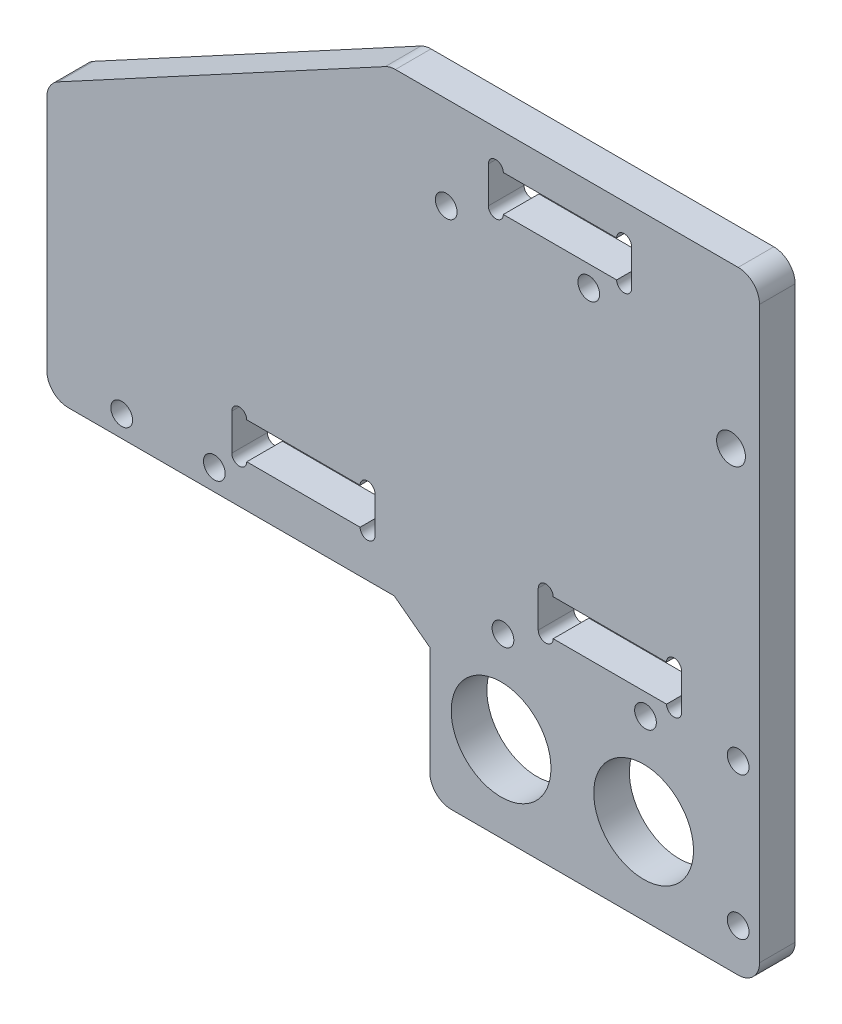
SolidWorks part; units mm, degrees
material "Thornel Mat VMA"
ref_plane "前视基准面" through (0, 0, 0) normal (0, 0, 1) x (1, 0, 0)
ref_plane "上视基准面" through (0, 0, 0) normal (0, 1, 0) x (1, 0, 0)
ref_plane "右视基准面" through (0, 0, 0) normal (1, 0, 0) x (0, 0, -1)
other "Configuration Table"
sketch "草图1" plane through (0, 0, 0) normal (0, 0, 1) x (1, 0, 0)
  line L0 (0, 0) -> (-46.2626, 16.8382)
  line L1 (-46.2626, 16.8382) -> (-46.2626, 27.95)
  line L2 (-46.2626, 27.95) -> (-86.2626, 27.95)
  line L3 (-86.2626, 27.95) -> (-100, 32.95)
  line L4 (-100, 32.95) -> (-100, 87)
  line L5 (-100, 87) -> (0, 87)
  line L6 (0, 87) -> (0, 0)
  line L11 (-127.5, 27.95) -> (-80, 27.95) construction
  dimension "D1" = 87
  dimension "D2" = 100
  dimension "D3" = 70
  dimension "D4" = 40
  dimension "D5" = 5
extrude "凸台-拉伸1" add sketch "草图1" along normal blind 5
sketch "草图4" plane through (0, 0, 0) normal (0, 0, -1) x (-1, 0, 0)
  line L1 (17.95, 81.05) -> (38.05, 81.05)
  line L2 (17.95, 81.05) -> (17.95, 75.95)
  line L3 (17.95, 75.95) -> (38.05, 75.95)
  line L4 (38.05, 81.05) -> (38.05, 75.95)
  line L5 (17.95, 81.05) -> (38.05, 75.95) construction
  line L6 (17.95, 75.95) -> (38.05, 81.05) construction
  line L7 (0, 0) -> (0, 87) construction
  line L8 (0, 87) -> (100, 87) construction
  point P0 (28, 78.5)
  dimension "D1" = 8.5
  dimension "D2" = 5.1
  dimension "D3" = 20.1
  dimension "D4" = 28
extrude "切除-拉伸3" cut sketch "草图4" against normal through all both and the other way through all
sketch "草图5" plane through (0, 0, 0) normal (0, 0, -1) x (-1, 0, 0)
  line L0 (37, 81.05) -> (37, 75.95) construction
  line L1 (38.05, 81.05) -> (17.95, 81.05) construction
  line L2 (17.95, 75.95) -> (38.05, 75.95) construction
  line L3 (38.05, 81.05) -> (38.05, 75.95)
  line L4 (35.95, 81.05) -> (35.95, 75.95)
  line L5 (38.05, 75.95) -> (38.05, 81.05) construction
  line L6 (28, 75.95) -> (28, 81.05) construction
  line L7 (19, 81.05) -> (19, 75.95) construction
  line L8 (17.95, 81.05) -> (17.95, 75.95)
  line L9 (20.05, 81.05) -> (20.05, 75.95)
  arc A0 (38.05, 81.05) -> (35.95, 81.05) centre (37, 81.05) ccw
  arc A1 (35.95, 75.95) -> (38.05, 75.95) centre (37, 75.95) ccw
  arc A2 (17.95, 81.05) -> (20.05, 81.05) centre (19, 81.05) cw
  arc A3 (20.05, 75.95) -> (17.95, 75.95) centre (19, 75.95) cw
  point P6 (37, 78.5)
  point P17 (19, 78.5)
  dimension "D1" = 1.05
extrude "切除-拉伸4" cut sketch "草图5" against normal through all
sketch "草图6" plane through (0, 0, 0) normal (0, 0, -1) x (-1, 0, 0)
  circle A0 centre (23.9626, 73) radius 1.525
  circle A1 centre (43.9626, 73) radius 1.525
  circle A2 centre (23.9626, 73) radius 1.25 construction
  circle A3 centre (43.9626, 73) radius 1.25 construction
  dimension "D1" = 3.05
extrude "切除-拉伸5" cut sketch "草图6" against normal through all both and the other way through all
sketch "草图7" plane through (0, 0, 0) normal (0, 0, -1) x (-1, 0, 0)
  line L0 (50, 87) -> (100, 59.975)
  line L1 (0, 87) -> (100, 87) construction
  line L2 (100, 87) -> (100, 32.95) construction
  line L3 (100, 59.975) -> (100, 87)
  line L4 (100, 87) -> (50, 87)
  dimension "D1" = 50
extrude "切除-拉伸6" cut sketch "草图7" against normal through all both and the other way through all
sketch "草图8" plane through (0, 0, 0) normal (0, 0, -1) x (-1, 0, 0)
  line L0 (100, 59.975) -> (100, 21.95)
  line L1 (100, 21.95) -> (46.2626, 21.95)
  line L3 (100, 59.975) -> (46.2626, 59.975)
  line L4 (46.2626, 59.975) -> (46.2626, 21.95)
  line L5 (80, 27.95) -> (127.5, 27.95) construction
  line L6 (46.2626, 27.95) -> (46.2626, 16.8382) construction
  dimension "D1" = 6
extrude "凸台-拉伸2" add sketch "草图8" against normal up to surface (5 mm away) up to face at (-53.5985, 42.4579, 5)
sketch "草图11" plane through (0, 0, 5) normal (0, 0, 1) x (1, 0, 0)
  circle A0 centre (-3, 6) radius 1.525
  circle A1 centre (-3, 26) radius 1.525
  circle A2 centre (-3, 6) radius 1.25 construction
  circle A3 centre (-3, 26) radius 1.25 construction
  dimension "D1" = 3.05
extrude "切除-拉伸9" cut sketch "草图11" against normal through all both and the other way through all
sketch "草图14" plane through (0, 0, 0) normal (0, 0, -1) x (-1, 0, 0)
  line L0 (0, 0) -> (0, 87) construction
  line L1 (0, 87) -> (50, 87) construction
  circle A0 centre (4, 63.5) radius 2.025
  circle A1 centre (4, 45.95) radius 2.025 construction
  dimension "D1" = 4.05
  dimension "D2" = 4.05
  dimension "D3" = 17.55
  dimension "D5" = 4
  dimension "D6" = 4
  dimension "D4" = 41.05
extrude "切除-拉伸10" cut sketch "草图14" against normal blind 10
sketch "草图15" plane through (0, 0, 0) normal (0, 0, -1) x (-1, 0, 0)
  line L1 (53.95, 33) -> (74.05, 33)
  line L2 (53.95, 33) -> (53.95, 27.9)
  line L3 (53.95, 27.9) -> (74.05, 27.9)
  line L4 (74.05, 33) -> (74.05, 27.9)
  line L5 (53.95, 33) -> (74.05, 27.9) construction
  line L6 (53.95, 27.9) -> (74.05, 33) construction
  line L7 (10.95, 27.9) -> (31.05, 27.9)
  line L8 (10.95, 27.9) -> (10.95, 33)
  line L9 (10.95, 33) -> (31.05, 33)
  line L10 (31.05, 27.9) -> (31.05, 33)
  line L11 (10.95, 27.9) -> (31.05, 33) construction
  line L12 (10.95, 33) -> (31.05, 27.9) construction
  line L13 (0, 0) -> (0, 87) construction
  line L14 (30, 33) -> (30, 27.9) construction
  line L15 (31.05, 33) -> (31.05, 27.9)
  line L16 (28.95, 33) -> (28.95, 27.9)
  line L17 (12, 33) -> (12, 27.9) construction
  line L18 (13.05, 33) -> (13.05, 27.9)
  line L19 (10.95, 33) -> (10.95, 27.9)
  line L20 (55, 33) -> (55, 27.9) construction
  line L21 (56.05, 33) -> (56.05, 27.9)
  line L22 (53.95, 33) -> (53.95, 27.9)
  line L23 (73, 33) -> (73, 27.9) construction
  line L24 (74.05, 33) -> (74.05, 27.9)
  line L25 (71.95, 33) -> (71.95, 27.9)
  line L26 (46.2626, 21.95) -> (100, 21.95) construction
  arc A0 (31.05, 33) -> (28.95, 33) centre (30, 33) ccw
  arc A1 (28.95, 27.9) -> (31.05, 27.9) centre (30, 27.9) ccw
  arc A2 (13.05, 33) -> (10.95, 33) centre (12, 33) ccw
  arc A3 (10.95, 27.9) -> (13.05, 27.9) centre (12, 27.9) ccw
  arc A4 (56.05, 33) -> (53.95, 33) centre (55, 33) ccw
  arc A5 (53.95, 27.9) -> (56.05, 27.9) centre (55, 27.9) ccw
  arc A6 (74.05, 33) -> (71.95, 33) centre (73, 33) ccw
  arc A7 (71.95, 27.9) -> (74.05, 27.9) centre (73, 27.9) ccw
  point P0 (64, 30.45)
  point P5 (21, 30.45)
  point P14 (30, 30.45)
  point P21 (12, 30.45)
  point P30 (55, 30.45)
  point P35 (73, 30.45)
  dimension "D6" = 1.05
  dimension "D7" = 1.05
  dimension "D8" = 1.05
  dimension "D9" = 1.05
  dimension "D1" = 5.1
  dimension "D2" = 8.5
  dimension "D3" = 20.1
  dimension "D4" = 64
  dimension "D5" = 21
extrude "切除-拉伸11" cut sketch "草图15" against normal through all contours L9 A2 | L18 L9 L8 L7 | L7 A3 | L9 L18 L7 L16 | L9 L16 L7 L10 | L1 A4 | L21 L1 L2 L3 | L3 A5 | L25 L1 L21 L3 | L1 L25 L3 L4 | L1 A6 | L3 A7
sketch "草图16" plane through (0, 0, 0) normal (0, 0, -1) x (-1, 0, 0)
  line L0 (0, 0) -> (0, 87) construction
  line L1 (13.05, 27.9) -> (28.95, 27.9) construction
  circle A0 centre (16, 24.95) radius 1.525
  circle A1 centre (36, 24.95) radius 1.525
  dimension "D1" = 16
  dimension "D2" = 3.05
  dimension "D3" = 2.95
  dimension "D4" = 3.05
  dimension "D5" = 20
extrude "切除-拉伸12" cut sketch "草图16" against normal through all both
sketch "草图17" plane through (0, 0, 0) normal (0, 0, -1) x (-1, 0, 0)
  line L0 (0, 86) -> (51.8501, 86)
  line L1 (0, 0) -> (0, 87) construction
  line L2 (100, 59.975) -> (50, 87) construction
  line L3 (51.8501, 86) -> (50, 87)
  line L4 (50, 87) -> (0, 87)
  line L5 (0, 87) -> (50, 87) construction
  line L6 (0, 87) -> (0, 86)
  dimension "D1" = 1
extrude "切除-拉伸13" cut sketch "草图17" against normal blind 10
sketch "草图18" plane through (0, 0, 5) normal (0, 0, 1) x (1, 0, 0)
  line L4 (-46.2626, 16.8382) -> (-46.2626, 0)
  line L5 (-46.2626, 0) -> (0, 0)
  line L6 (0, 0) -> (-46.2626, 16.8382)
extrude "凸台-拉伸3" add sketch "草图18" against normal up to surface (5 mm away) up to face at (-17.525, 24.95, 0)
sketch "草图19" plane through (0, 0, 5) normal (0, 0, 1) x (1, 0, 0)
  line L0 (-46.2626, 6.95) -> (-66.2626, 21.95)
  line L1 (-46.2626, 21.95) -> (-46.2626, 0) construction
  line L2 (-46.2626, 21.95) -> (-100, 21.95) construction
  line L3 (-66.2626, 21.95) -> (-46.2626, 21.95)
  line L4 (-46.2626, 21.95) -> (-46.2626, 6.95)
  dimension "D1" = 20
  dimension "D2" = 15
extrude "凸台-拉伸4" add sketch "草图19" against normal up to surface (5 mm away) up to face at (-17.525, 24.95, 0)
fillet "圆角1" radius 3 6 edges at (-46.2626, 0, 2.5) (0, 0, 2.5) (0, 86, 2.5) (-51.8501, 86, 2.5) (-100, 59.975, 2.5) (-100, 21.95, 2.5)
sketch "草图20" plane through (0, 0, 5) normal (0, 0, 1) x (1, 0, 0)
  line L0 (-43.2626, 0) -> (-3, 0) construction
  line L1 (-46.2626, 6.95) -> (-46.2626, 3) construction
  circle A0 centre (-36.2626, 12) radius 7
  circle A1 centre (-16.2626, 12) radius 7
  dimension "D1" = 14
  dimension "D3" = 12
  dimension "D4" = 10
  dimension "D2" = 20
extrude "切除-拉伸14" cut sketch "草图20" against normal up to surface (5 mm away) up to face at (-50.5337, 38.6081, 0)
sketch "草图21" plane through (0, 0, 5) normal (0, 0, 1) x (1, 0, 0)
  circle A0 centre (-89.5, 24.95) radius 1.525
  circle A1 centre (-76.5, 24.95) radius 1.525
  circle A2 centre (-89.5, 24.95) radius 1.25 construction
  circle A3 centre (-76.5, 24.95) radius 1.25 construction
  dimension "D1" = 3.05
extrude "切除-拉伸15" cut sketch "草图21" against normal blind 8
sketch "草图23" plane through (0, 0, 0) normal (0, 0, -1) x (-1, 0, 0)
  line L0 (46.2626, 6.95) -> (46.2626, 21.95)
  line L1 (66.2626, 21.95) -> (46.2626, 21.95)
  line L2 (46.2626, 6.95) -> (66.2626, 21.95) construction
  line L3 (46.2626, 6.95) -> (66.2626, 21.95)
  line L4 (40.8626, 14.15) -> (60.8626, 29.15)
  line M11 (46.2626, 6.95) -> (66.2626, 21.95)
  dimension "D1" = 9
extrude "切除-拉伸17" cut sketch "草图23" against normal through all contours L4 L0 L1 M11
